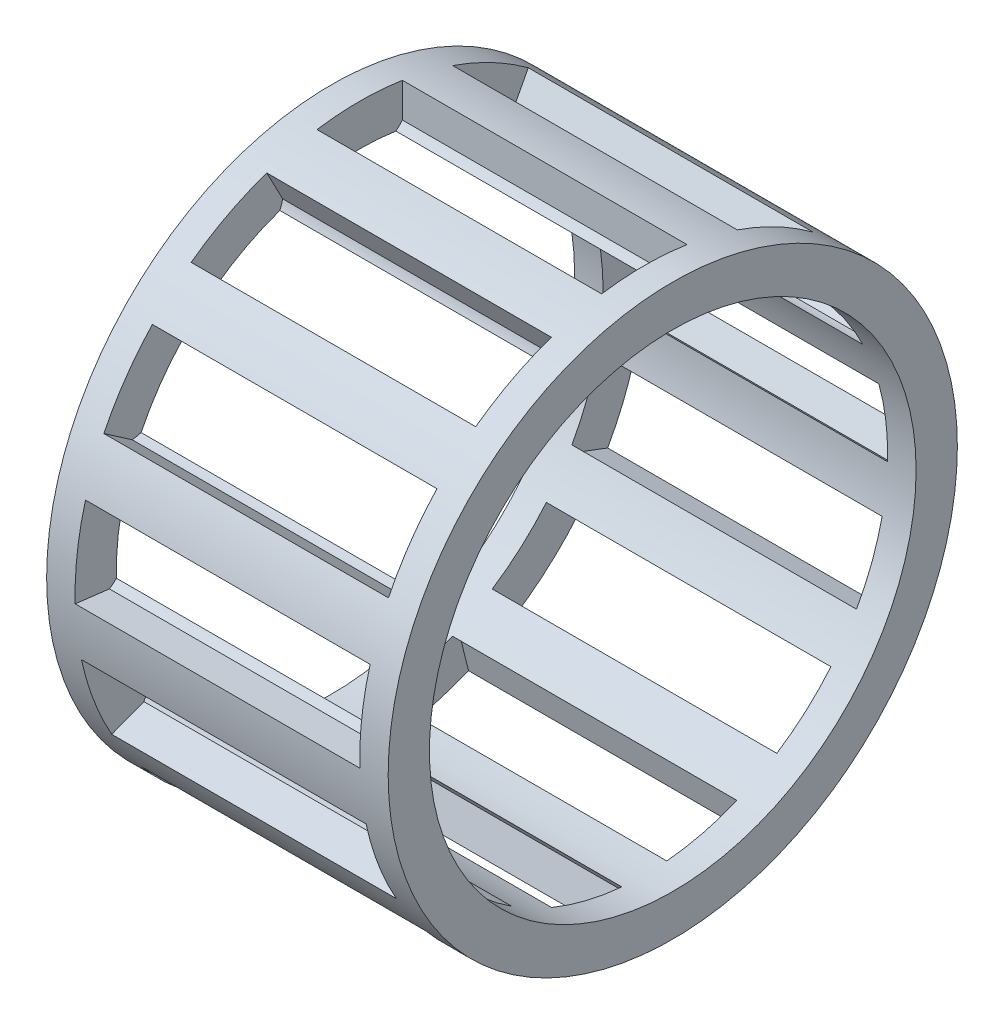
SolidWorks part; units mm, degrees
ref_plane "Piano frontale" through (0, 0, 0) normal (0, 0, 1) x (1, 0, 0)
ref_plane "Piano superiore" through (0, 0, 0) normal (0, 1, 0) x (1, 0, 0)
ref_plane "Piano destro" through (0, 0, 0) normal (1, 0, 0) x (0, 0, -1)
sketch "Schizzo4" plane through (0, 0, 0) normal (0, 0, 1) x (1, 0, 0)
  line L0 (-6, 8.55) -> (6, 8.55)
  line L1 (-6, 8.55) -> (-6, 10)
  line L2 (-6, 10) -> (6, 10)
  line L3 (6, 10) -> (6, 8.55)
  line L4 (0, 0) -> (-5.2484, 0) construction
  dimension "D1" = 12
  dimension "D3" = 1.45
revolve "Rivoluzione1" add sketch "Schizzo4" angle 360 about L4
sketch "Schizzo6" plane through (0, 0, 0) normal (1, 0, 0) x (0, 0, -1)
  line L0 (-1.5, 10) -> (-1.5, 8.6771)
  line L1 (1.5, 10) -> (1.5, 8.6771)
  arc A0 (-1.5, 8.6771) -> (1.5, 8.6771) centre (0, 10) ccw
  arc A1 (1.5, 10) -> (-1.5, 10) centre (0, 10) ccw
  dimension "D1" = 4
  dimension "D2" = 3
extrude "Taglio-Estrusione1" cut sketch "Schizzo6" against normal blind 5 and the other way blind 5
pattern_circular "RipetizioneCircolare1" count 13 over 360 about axis through (0, 0, 0) along (1, 0, 0) of "Taglio-Estrusione1"
